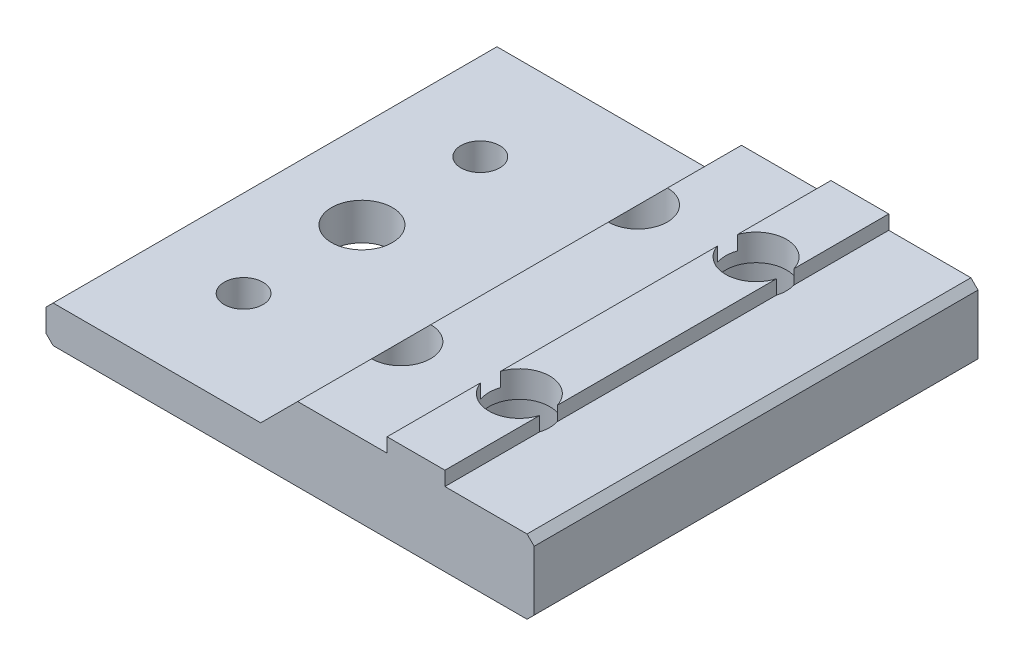
SolidWorks part; units mm, degrees
ref_plane "Front Plane" through (0, 0, 0) normal (0, 0, 1) x (1, 0, 0)
ref_plane "Top Plane" through (0, 0, 0) normal (0, 1, 0) x (1, 0, 0)
ref_plane "Right Plane" through (0, 0, 0) normal (1, 0, 0) x (0, 0, -1)
sketch "Sketch1" plane through (0, 0, 0) normal (0, 0, 1) x (1, 0, 0)
  line L0 (55.5247, 16.9524) -> (55.5247, 18.4764)
  line L1 (45.9235, 16.9524) -> (55.5247, 16.9524)
  line L2 (55.5247, 18.4764) -> (61.7308, 18.4764)
  line L3 (41.9611, 12.99) -> (45.9235, 16.9524)
  line L4 (61.7293, 16.9531) -> (61.7308, 18.4764)
  line L5 (19.6853, 12.99) -> (41.9611, 12.99)
  line L6 (61.7293, 16.9531) -> (70.5431, 16.9531)
  line L7 (18.9233, 9.7896) -> (18.9233, 12.228)
  line L8 (19.6853, 12.99) -> (18.9233, 12.228)
  line L9 (18.9233, 9.7896) -> (19.6853, 9.0276)
  line L10 (19.6853, 9.0276) -> (70.5439, 9.0276)
  line L11 (71.3051, 9.7896) -> (70.5439, 9.0276)
  line L12 (71.3051, 9.7896) -> (71.3051, 16.1904)
  line L13 (70.5431, 16.9531) -> (71.3051, 16.1904)
  dimension "D1" = 90
  dimension "D2" = 90
extrude "Extrude1" add sketch "Sketch1" along normal blind 47.625
sketch "Sketch2" plane through (0, 9.0276, 0) normal (0, -1, 0) x (1, 0, 0)
  line L2 (58.6051, 47.625) -> (58.6051, 0)
  line L3 (58.6051, 47.625) -> (58.6051, 0)
  line L4 (19.6853, 11.1125) -> (70.5439, 11.1125)
  line L5 (19.6853, 36.5125) -> (70.5439, 36.5125)
  line L6 (19.6853, 36.5125) -> (70.5439, 36.5125)
  circle A0 centre (58.6051, 36.5125) radius 3.2639
  circle A1 centre (58.6051, 11.1125) radius 3.2639
  dimension "D1" = 12.7
  dimension "D2" = 11.1125
  dimension "D3" = 25.4
extrude "Cut-Extrude1" cut sketch "Sketch2" against normal blind 47.625 contours L3 A0 L6 | L6 A0 L3 | L3 A0 L6 | L6 A0 L3 | L4 A1 L3 | L3 A1 L4 | L4 A1 L3 | L3 A1 L4
sketch "Sketch3" plane through (0, 9.0276, 0) normal (0, -1, 0) x (1, 0, 0)
  circle A0 centre (58.6051, 36.5125) radius 5.1562
  circle A1 centre (58.6051, 11.1125) radius 5.1562
extrude "Cut-Extrude2" cut sketch "Sketch3" against normal blind 6.604
sketch "Sketch4" plane through (0, 9.0276, 0) normal (0, -1, 0) x (1, 0, 0)
  line L1 (19.6853, 36.5125) -> (70.5439, 36.5125) construction
  line L4 (19.6853, 11.1125) -> (70.5439, 11.1125) construction
  circle A0 centre (45.9051, 36.5125) radius 3.175
  circle A1 centre (45.9051, 11.1125) radius 3.175
extrude "Cut-Extrude3" cut sketch "Sketch4" against normal through all
sketch "Sketch5" plane through (0, 9.0276, 0) normal (0, -1, 0) x (1, 0, 0)
  line L1 (19.6853, 36.5125) -> (70.5439, 36.5125) construction
  line L4 (19.6853, 11.1125) -> (70.5439, 11.1125) construction
  circle A0 centre (29.0141, 36.5125) radius 2.0828
  circle A1 centre (29.0141, 11.1125) radius 2.0828
  circle A2 centre (29.0141, 23.8125) radius 3.2639
extrude "Cut-Extrude4" cut sketch "Sketch5" against normal through all
